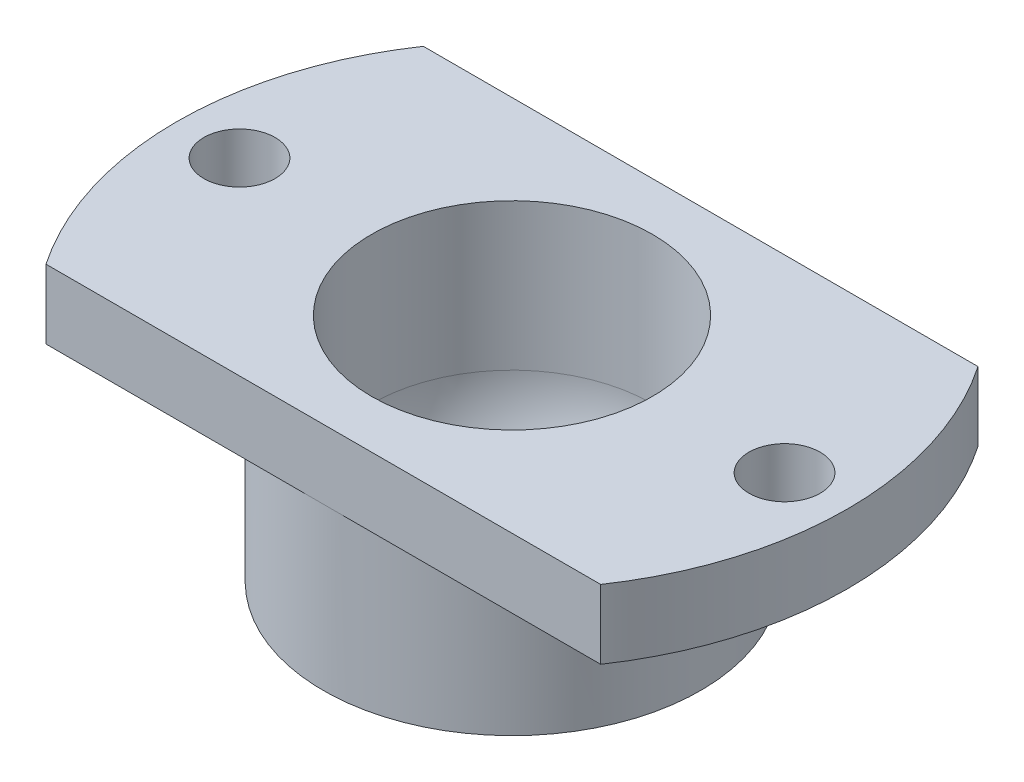
SolidWorks part; units mm, degrees
material "ABS"
ref_plane "Front Plane" through (0, 0, 0) normal (0, 0, 1) x (1, 0, 0)
ref_plane "Top Plane" through (0, 0, 0) normal (0, 1, 0) x (1, 0, 0)
ref_plane "Right Plane" through (0, 0, 0) normal (1, 0, 0) x (0, 0, -1)
sketch "Sketch1" plane through (0, 0, 0) normal (1, 0, 0) x (0, 0, -1)
  line L0 (-16, 7) -> (-6.7, 7)
  line L1 (-16, 7) -> (-16, 3.7)
  line L2 (0, 0) -> (0, 10.3505) construction
  line L3 (-16, 3.7) -> (-9, 3.7)
  line L4 (-6.7, 0) -> (-6.7, 7)
  line L6 (-9, -4) -> (-5.3749, -4)
  line L7 (-9, -4) -> (-9, 3.7)
  line L8 (-16, 7) -> (-6.7, 7)
  arc A0 (-6.7, 0) -> (-5.3749, -4) centre (0, 0) ccw
  dimension "D1" = 16
  dimension "D2" = 6.7
  dimension "D3" = 3.7
  dimension "D4" = 3.3
  dimension "D5" = 7
  dimension "D6" = 4
revolve "Revolve1" add sketch "Sketch1" angle 360 about L2
hole_wizard "M3 Clearance Hole1" positions "Sketch4" profile "Sketch3" hole size "M3" standard "ISO"
sketch "Sketch4" plane through (0, 3.7, 0) normal (0, -1, 0) x (-1, 0, 0)
  point P0 (13, 0)
  dimension "D1" = 13
sketch "Sketch3" plane through (-13, 3.7, 0) normal (1, 0, 0) x (0, 0, -1)
  line L0 (0, 0) -> (0, 11.0215)
  line L1 (0, 11.0215) -> (1.7, 10)
  line L2 (1.7, 10) -> (1.7, 0)
  line L5 (1.7, 0) -> (0, 0)
  line L10 (0, 11.0215) -> (-1.7, 10) construction
  line L11 (0, -6.35) -> (0, 107.95) construction
  dimension "Hole Dia." = 3.4
  dimension "Hole Depth" = 10
  dimension "Drill Angle" = 118
pattern_circular "CirPattern2" count 2 over 360 about axis through (0, 0, 0) along (0, 1, 0) of "M3 Clearance Hole1"
sketch "Sketch5" plane through (0, 3.7, 0) normal (0, -1, 0) x (1, 0, 0)
  line L1 (-17.0763, 9) -> (20.9148, 9)
  line L2 (-17.0763, 9) -> (-17.0763, -9)
  line L3 (-17.0763, -9) -> (20.9148, -9)
  line L4 (20.9148, 9) -> (20.9148, -9)
  line L5 (-23.7253, 17.7727) -> (26.7016, 17.7727)
  line L6 (-23.7253, 17.7727) -> (-23.7253, -19.4883)
  line L7 (-23.7253, -19.4883) -> (26.7016, -19.4883)
  line L8 (26.7016, 17.7727) -> (26.7016, -19.4883)
  circle A0 centre (0, 0) radius 9 construction
  circle A1 centre (0, 0) radius 9 construction
extrude "Cut-Extrude1" cut sketch "Sketch5" against normal through all
